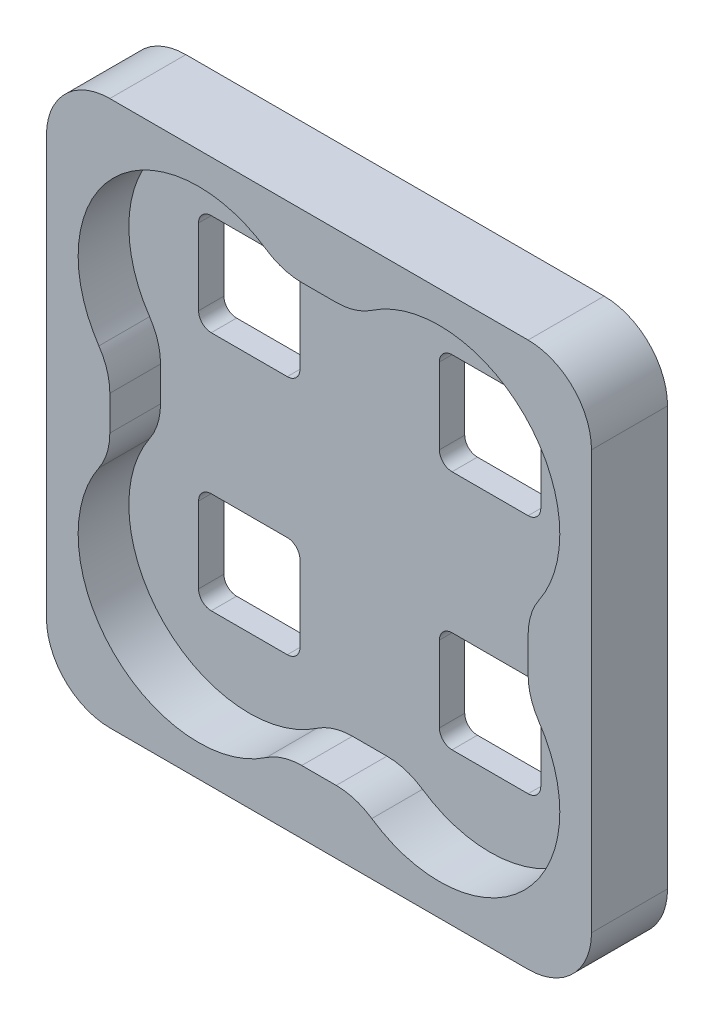
SolidWorks part; units mm, degrees
ref_plane "Płaszczyzna przednia" through (0, 0, 0) normal (0, 0, 1) x (1, 0, 0)
ref_plane "Płaszczyzna górna" through (0, 0, 0) normal (0, 1, 0) x (1, 0, 0)
ref_plane "Płaszczyzna prawa" through (0, 0, 0) normal (1, 0, 0) x (0, 0, -1)
sketch "Szkic1" plane through (0, 0, 0) normal (0, 0, 1) x (1, 0, 0)
  line L1 (-16.5, 21.5) -> (16.5, 21.5)
  line L2 (-21.5, 16.5) -> (-21.5, -16.5)
  line L3 (-16.5, -21.5) -> (16.5, -21.5)
  line L4 (21.5, 16.5) -> (21.5, -16.5)
  line L5 (-21.5, 21.5) -> (21.5, -21.5) construction
  line L6 (-21.5, -21.5) -> (21.5, 21.5) construction
  arc A0 (-16.5, -21.5) -> (-21.5, -16.5) centre (-16.5, -16.5) cw
  arc A1 (16.5, -21.5) -> (21.5, -16.5) centre (16.5, -16.5) ccw
  arc A2 (16.5, 21.5) -> (21.5, 16.5) centre (16.5, 16.5) cw
  arc A3 (-16.5, 21.5) -> (-21.5, 16.5) centre (-16.5, 16.5) ccw
  point P0 (0, 0)
  dimension "D3" = 5
  dimension "D1" = 43
  dimension "D2" = 43
extrude "Dodanie-wyciągnięcie1" add sketch "Szkic1" along normal blind 6
sketch "Szkic2" plane through (0, 0, 6) normal (0, 0, 1) x (1, 0, 0)
  line L0 (-20.0355, 20.0355) -> (20.0355, -20.0355) construction
  line L1 (-20.0355, -20.0355) -> (20.0355, 20.0355) construction
  line L2 (-16.5, 1.3606) -> (-16.5, -1.3606)
  line L3 (-1.3606, 16.5) -> (1.3606, 16.5)
  line L4 (-1.3606, -16.5) -> (1.3606, -16.5)
  line L5 (16.5, 1.3606) -> (16.5, -1.3606)
  line L6 (-21.5, 16.5) -> (-21.5, -16.5) construction
  line L7 (16.5, 21.5) -> (-16.5, 21.5) construction
  line L8 (21.5, -16.5) -> (21.5, 16.5) construction
  line L9 (-16.5, -21.5) -> (16.5, -21.5) construction
  arc A4 (-16.5, 21.5) -> (-21.5, 16.5) centre (-16.5, 16.5) ccw construction
  arc A5 (21.5, 16.5) -> (16.5, 21.5) centre (16.5, 16.5) ccw construction
  circle A6 centre (-9.5, 9.5) radius 9.5 construction
  circle A7 centre (9.5, 9.5) radius 9.5 construction
  circle A8 centre (9.5, -9.5) radius 9.5 construction
  circle A9 centre (-9.5, -9.5) radius 9.5 construction
  arc A10 (4.1673, 17.3621) -> (17.3621, 4.1673) centre (9.5, 9.5) cw
  arc A11 (17.3621, -4.1673) -> (4.1673, -17.3621) centre (9.5, -9.5) cw
  arc A12 (-4.1673, -17.3621) -> (-17.3621, -4.1673) centre (-9.5, -9.5) cw
  arc A13 (-17.3621, 4.1673) -> (-4.1673, 17.3621) centre (-9.5, 9.5) cw
  arc A14 (-16.5, -1.3606) -> (-17.3621, -4.1673) centre (-21.5, -1.3606) cw
  arc A15 (-1.3606, -16.5) -> (-4.1673, -17.3621) centre (-1.3606, -21.5) ccw
  arc A16 (1.3606, -16.5) -> (4.1673, -17.3621) centre (1.3606, -21.5) cw
  arc A17 (17.3621, -4.1673) -> (16.5, -1.3606) centre (21.5, -1.3606) cw
  arc A18 (16.5, 1.3606) -> (17.3621, 4.1673) centre (21.5, 1.3606) cw
  arc A19 (4.1673, 17.3621) -> (1.3606, 16.5) centre (1.3606, 21.5) cw
  arc A20 (-4.1673, 17.3621) -> (-1.3606, 16.5) centre (-1.3606, 21.5) ccw
  arc A21 (-16.5, 1.3606) -> (-17.3621, 4.1673) centre (-21.5, 1.3606) ccw
  point P13 (0, 9.5)
  point P17 (0, -9.5)
  point P21 (9.5, 0)
  point P26 (-9.5, 0)
  point P44 (-3.0774, -16.5)
  point P48 (16.5, -3.0774)
  point P51 (16.5, 3.0774)
  point P54 (3.0774, 16.5)
  point P57 (-3.0774, 16.5)
  point P60 (-16.5, 3.0774)
  dimension "D1" = 19
  dimension "D2" = 19
  dimension "D3" = 19
  dimension "D4" = 19
  dimension "D5" = 19
  dimension "D6" = 5
  dimension "D10" = 5
  dimension "D7" = 5
  dimension "D8" = 5
  dimension "D9" = 5
extrude "Wytnij-wyciągnięcie2" cut sketch "Szkic2" against normal blind 4 contours A13 A20 L3 A19 A10 A18 L5 A17 A11 A16 L4 A15 A12 A14 L2 A21
sketch "Szkic3" plane through (0, 0, 2) normal (0, 0, 1) x (1, 0, 0)
  line L1 (6.5, -5.5) -> (12.5, -5.5)
  line L2 (5.5, -6.5) -> (5.5, -12.5)
  line L3 (6.5, -13.5) -> (12.5, -13.5)
  line L4 (13.5, -6.5) -> (13.5, -12.5)
  line L5 (5.5, -5.5) -> (13.5, -13.5) construction
  line L6 (5.5, -13.5) -> (13.5, -5.5) construction
  line L7 (6.5, 13.5) -> (12.5, 13.5)
  line L8 (5.5, 12.5) -> (5.5, 6.5)
  line L9 (6.5, 5.5) -> (12.5, 5.5)
  line L10 (13.5, 12.5) -> (13.5, 6.5)
  line L11 (5.5, 13.5) -> (13.5, 5.5) construction
  line L12 (5.5, 5.5) -> (13.5, 13.5) construction
  line L13 (-12.5, -5.5) -> (-6.5, -5.5)
  line L14 (-13.5, -6.5) -> (-13.5, -12.5)
  line L15 (-12.5, -13.5) -> (-6.5, -13.5)
  line L16 (-5.5, -6.5) -> (-5.5, -12.5)
  line L17 (-13.5, -5.5) -> (-5.5, -13.5) construction
  line L18 (-13.5, -13.5) -> (-5.5, -5.5) construction
  line L19 (-12.5, 13.5) -> (-6.5, 13.5)
  line L20 (-13.5, 12.5) -> (-13.5, 6.5)
  line L21 (-12.5, 5.5) -> (-6.5, 5.5)
  line L22 (-5.5, 12.5) -> (-5.5, 6.5)
  line L23 (-13.5, 13.5) -> (-5.5, 5.5) construction
  line L24 (-13.5, 5.5) -> (-5.5, 13.5) construction
  arc A0 (12.5, 5.5) -> (13.5, 6.5) centre (12.5, 6.5) ccw
  arc A1 (12.5, 13.5) -> (13.5, 12.5) centre (12.5, 12.5) cw
  arc A2 (6.5, 13.5) -> (5.5, 12.5) centre (6.5, 12.5) ccw
  arc A3 (5.5, 6.5) -> (6.5, 5.5) centre (6.5, 6.5) ccw
  arc A4 (5.5, -12.5) -> (6.5, -13.5) centre (6.5, -12.5) ccw
  arc A5 (12.5, -13.5) -> (13.5, -12.5) centre (12.5, -12.5) ccw
  arc A6 (12.5, -5.5) -> (13.5, -6.5) centre (12.5, -6.5) cw
  arc A7 (6.5, -5.5) -> (5.5, -6.5) centre (6.5, -6.5) ccw
  arc A8 (-12.5, -13.5) -> (-13.5, -12.5) centre (-12.5, -12.5) cw
  arc A9 (-6.5, -13.5) -> (-5.5, -12.5) centre (-6.5, -12.5) ccw
  arc A10 (-6.5, -5.5) -> (-5.5, -6.5) centre (-6.5, -6.5) cw
  arc A11 (-12.5, -5.5) -> (-13.5, -6.5) centre (-12.5, -6.5) ccw
  arc A12 (-13.5, 6.5) -> (-12.5, 5.5) centre (-12.5, 6.5) ccw
  arc A13 (-6.5, 5.5) -> (-5.5, 6.5) centre (-6.5, 6.5) ccw
  arc A14 (-6.5, 13.5) -> (-5.5, 12.5) centre (-6.5, 12.5) cw
  arc A15 (-12.5, 13.5) -> (-13.5, 12.5) centre (-12.5, 12.5) ccw
  point P0 (9.5, -9.5)
  point P6 (9.5, 9.5)
  point P12 (-9.5, -9.5)
  point P18 (-9.5, 9.5)
  dimension "D9" = 1
  dimension "D1" = 8
  dimension "D2" = 8
  dimension "D3" = 8
  dimension "D4" = 8
  dimension "D5" = 8
  dimension "D6" = 8
  dimension "D7" = 8
  dimension "D8" = 8
extrude "Wytnij-wyciągnięcie3" cut sketch "Szkic3" against normal blind 2
